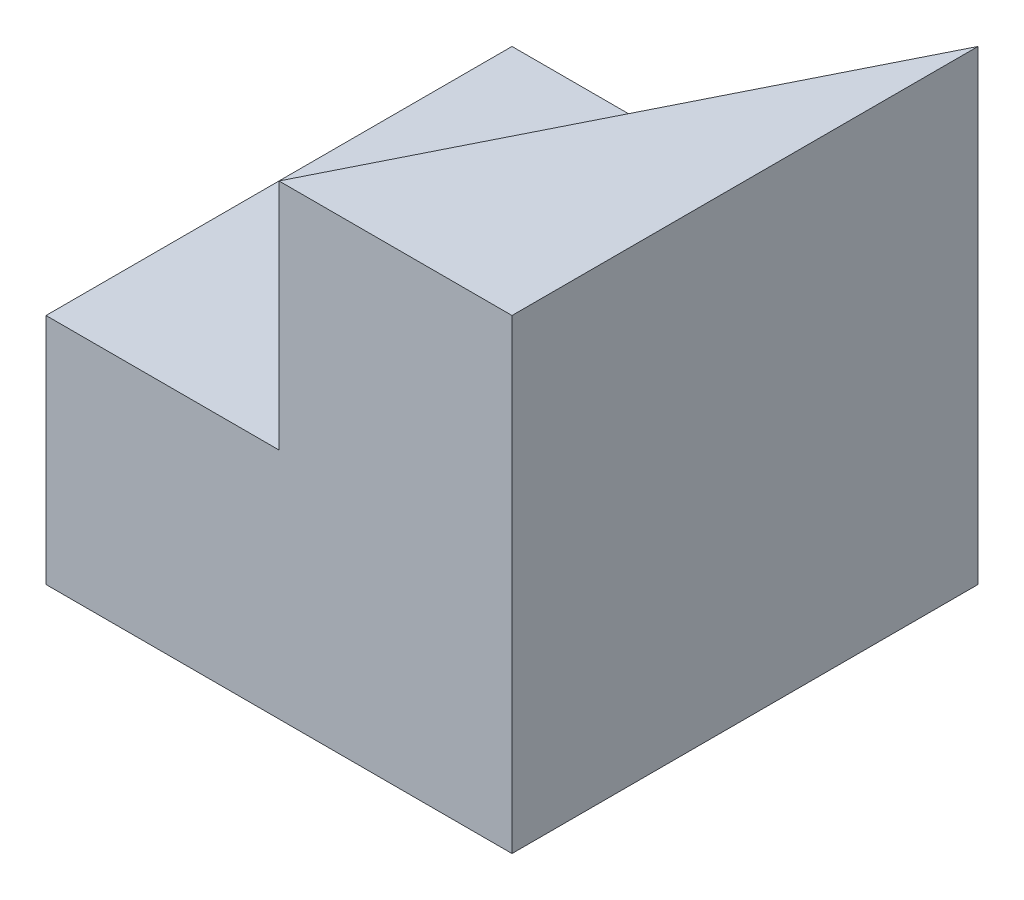
SolidWorks part; units mm, degrees
ref_plane "Front Plane" through (0, 0, 0) normal (0, 0, 1) x (1, 0, 0)
ref_plane "Top Plane" through (0, 0, 0) normal (0, 1, 0) x (1, 0, 0)
ref_plane "Right Plane" through (0, 0, 0) normal (1, 0, 0) x (0, 0, -1)
sketch "Sketch1" plane through (0, 0, 0) normal (0, 0, 1) x (1, 0, 0)
  line L1 (0, 0) -> (40, 0)
  line L2 (0, 0) -> (0, 40)
  line L3 (0, 40) -> (40, 40)
  line L4 (40, 0) -> (40, 40)
  dimension "D1" = 40
  dimension "D2" = 40
extrude "Boss-Extrude1" add sketch "Sketch1" along normal blind 40
sketch "Sketch2" plane through (0, 0, 40) normal (0, 0, 1) x (1, 0, 0)
  line L1 (0, 40) -> (20, 40)
  line L2 (0, 40) -> (0, 20)
  line L3 (0, 20) -> (20, 20)
  line L4 (20, 40) -> (20, 20)
  dimension "D1" = 20
  dimension "D2" = 20
extrude "Cut-Extrude1" cut sketch "Sketch2" against normal blind 40
sketch "Sketch3" plane through (0, 40, 0) normal (0, 1, 0) x (1, 0, 0)
  line L0 (20, -40) -> (40, 0)
  line L1 (40, 0) -> (20, 0)
  line L2 (20, 0) -> (20, -40)
extrude "Cut-Extrude2" cut sketch "Sketch3" against normal blind 20
